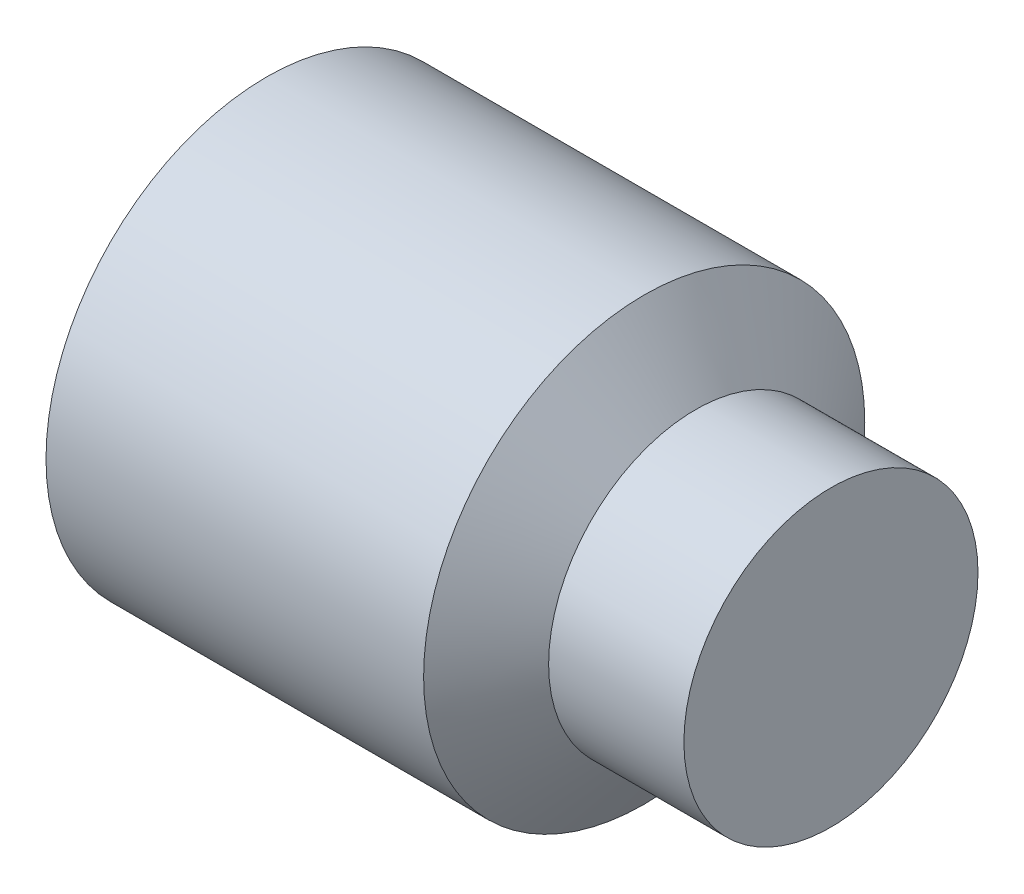
SolidWorks part; units mm, degrees
ref_plane "Plane1" through (0, 0, 0) normal (0, 0, 1) x (1, 0, 0)
ref_plane "Plane2" through (0, 0, 0) normal (0, 1, 0) x (1, 0, 0)
ref_plane "Plane3" through (0, 0, 0) normal (1, 0, 0) x (0, 0, -1)
sketch "BodySke" plane through (0, 0, 0) normal (0, 0, 1) x (1, 0, 0)
  line L0 (0, 0) -> (0, 1.2195)
  line L1 (0, 1.2195) -> (0.1619, 1.5)
  line L2 (0.1619, 1.5) -> (2.7299, 1.5)
  line L3 (2.7299, 1.5) -> (3.08, 1)
  line L4 (4, 0) -> (0, 0)
  line L5 (-12.7, 0) -> (88.9, 0) construction
  line L6 (3.08, 1) -> (4, 1)
  line L7 (4, 1) -> (4, 0)
  line L8 (0, -1.2195) -> (0.1619, -1.5) construction
  line L9 (3.08, -1) -> (4, -1) construction
  line L10 (0.5, 15.875) -> (0.5, -3.175) construction
  dimension "D1" = 35
  dimension "Length" = 4
  dimension "Diameter" = 3
  dimension "Drive_ch_ang" = 60
  dimension "Minor_dia" = 2.439
  dimension "Dog_dia" = 2
  dimension "Dog_len" = 0.92
  dimension "Advance" = 0.5
revolve "BaseBody" add sketch "BodySke" angle 360 about L5
cosmetic thread "ThreadCosmetic" [suppressed] parameters "Thread_minor"=2.439
sketch "Sketch2" plane through (0, 0, 0) normal (-1, 0, 0) x (0, 0, 1)
  line L0 (0.433, 0.75) -> (-0.433, 0.75)
  line L1 (-0.433, 0.75) -> (-0.866, 0)
  line L2 (0.433, 0.75) -> (0.866, 0)
  line L3 (0.433, -0.75) -> (0.866, 0)
  line L4 (0.433, -0.75) -> (-0.433, -0.75)
  line L5 (-0.433, -0.75) -> (-0.866, 0)
  dimension "Hex_size" = 1.5
  dimension "D2" = 0.75
  dimension "D3" = 0.75
extrude "Hex" cut sketch "Sketch2" against normal blind 2
sketch "Sketch4" [suppressed] plane through (0, 4.7709, -0.5249) normal (-1, 0, 0) x (0, 0, 1)
  line L0 (0.5249, -4.7709) -> (8.1959, -4.7709)
  line L1 (0.5249, -4.7709) -> (6.6732, -1.2211) construction
  line L2 (0.5249, -4.7709) -> (4.3604, 1.8724)
  line L3 (6.7899, -3.1774) -> (7.8687, -2.5545)
  line L4 (5.0374, -0.142) -> (6.1162, 0.4809)
  arc A0 (6.7899, -3.1774) -> (5.0374, -0.142) centre (0.5249, -4.7709) ccw
  arc A1 (8.1959, -4.7709) -> (7.8687, -2.5545) centre (0.5249, -4.7709) ccw
  arc A2 (4.3604, 1.8724) -> (6.1162, 0.4809) centre (0.5249, -4.7709) cw
  circle A3 centre (0.5249, -4.7709) radius 6.4645 construction
  circle A4 centre (0.5249, -4.7709) radius 7.671 construction
  dimension "D1" = 30
  dimension "Spline_n_dim" = 1.295
  dimension "Spline_m_dim" = 1.575
  dimension "Spline_a_dim" = 60
  dimension "D3" = 0.178
  dimension "Spline_p_dim" = 0.356
extrude "Spline6" [suppressed] cut sketch "Sketch4" against normal blind 1.2
pattern_circular "CirPattern1" [suppressed] count 6 every 60 about axis through (-12.7, 0, 0) along (1, 0, 0)
sketch "Sketch5" [suppressed] plane through (0, 0.4822, 7.7588) normal (-1, 0, 0) x (0, 0, 1)
  line L0 (-7.7588, -0.4822) -> (-0.0878, -0.4822)
  line L1 (-7.7588, -0.4822) -> (-2.7387, 4.538) construction
  line L2 (-7.7588, -0.4822) -> (-7.7588, 7.1888)
  line L3 (-1.9485, 2.8497) -> (-1.2389, 3.5594)
  line L4 (-4.4269, 5.3281) -> (-3.7173, 6.0378)
  line L5 (-4.4269, 5.3281) -> (-1.9485, 2.8497)
  arc A1 (-0.0878, -0.4822) -> (-1.2389, 3.5594) centre (-7.7588, -0.4822) ccw
  arc A2 (-7.7588, 7.1888) -> (-3.7173, 6.0378) centre (-7.7588, -0.4822) cw
  circle A3 centre (-7.7588, -0.4822) radius 6.4645 construction
  circle A4 centre (-7.7588, -0.4822) radius 7.671 construction
  dimension "D1" = 45
  dimension "Spline_n_dim" = 1.295
  dimension "Spline_m_dim" = 1.575
  dimension "Spline_a_dim" = 90
  dimension "D3" = 0.178
  dimension "Spline_p_dim" = 0.356
extrude "Spline4" [suppressed] cut sketch "Sketch5" against normal blind 1.2
pattern_circular "CirPattern2" [suppressed] count 4 every 90 about axis through (-12.7, 0, 0) along (1, 0, 0)
sketch "ThdSchSke" [suppressed] plane through (0, 0, 0) normal (0, 0, 1) x (1, 0, 0)
  line L0 (0.9515, -10.352) -> (-0.2025, -12)
  line L1 (0.9515, -10.352) -> (2.1054, -12)
  line L2 (2.1054, -12) -> (2.1054, -15)
  line L3 (-3.175, 0) -> (5.1513, 0) construction
  line L4 (0.9515, 12) -> (0.9515, -12) construction
  line L5 (2.1054, -15) -> (-0.2025, -15)
  line L6 (-0.2025, -15) -> (-0.2025, -12)
  dimension "Thread_minor" = 2.439
  dimension "Diameter" = 3
  dimension "SideAngle" = 55
  dimension "VeeAngle" = 70
  dimension "Overcut" = 3.75
revolve "ThreadSchematic" [suppressed] cut sketch "ThdSchSke" angle 360 about L3
pattern_linear "ThdSchPat" [suppressed]
equation "\"D2@Sketch2\" = \"Hex_size@Sketch2\" / 2"
equation "\"D3@Sketch2\" = \"Hex_size@Sketch2\" / 2"
equation "\"Thread_minor@ThreadCosmetic\" = \"Minor_dia@BodySke\""
equation "\"D1@Sketch4\" = \"Spline_a_dim@Sketch4\" / 2"
equation "\"D3@Sketch4\" = \"Spline_p_dim@Sketch4\" / 2"
equation "\"D2@CirPattern1\" = \"Spline_a_dim@Sketch4\""
equation "\"Num_teeth@CirPattern1\" = 360 / \"D2@CirPattern1\""
equation "\"Spline_a_dim@Sketch5\" = 90"
equation "\"Spline_p_dim@Sketch5\" = \"Spline_p_dim@Sketch4\""
equation "\"Spline_m_dim@Sketch5\" = \"Spline_m_dim@Sketch4\""
equation "\"Spline_n_dim@Sketch5\" = \"Spline_n_dim@Sketch4\""
equation "\"D1@Sketch5\" = \"Spline_a_dim@Sketch5\" / 2"
equation "\"D3@Sketch5\" = \"Spline_p_dim@Sketch5\" / 2"
equation "\"Key_eng@Spline4\" = \"Key_eng@Spline6\""
equation "\"Thread_minor@ThdSchSke\" = \"Thread_minor@ThreadCosmetic\""
equation "\"Diameter@ThdSchSke\" = \"Diameter@BodySke\""
equation "\"Overcut@ThdSchSke\" = \"Diameter@BodySke\" * 1.25"
equation "\"Num_threads@ThdSchPat\" = int( (\"Length@BodySke\" - ( ( ( \"Diameter@BodySke\" - \"Minor_dia@BodySke\" ) * 0.5 ) / tan( \"Drive_ch_ang@BodySke\" * 0.017453292 ) ) - \"Dog_len@BodySke\" ) / \"Advance@BodySke\" + 0.999 )  + 1"
equation "\"Advance@ThdSchPat\" = (\"Length@BodySke\" - ( ( ( \"Diameter@BodySke\" - \"Minor_dia@BodySke\" ) * 0.5 ) / tan( \"Drive_ch_ang@BodySke\" * 0.017453292 ) ) - \"Dog_len@BodySke\" ) /  (\"Num_threads@ThdSchPat\" - 1) 'relax it"
equation "\"Num_threads@ThdSchPat\" = \"Num_threads@ThdSchPat\" - sgn( \"Num_threads@ThdSchPat\" - 1) '---chamfered tips only---"
